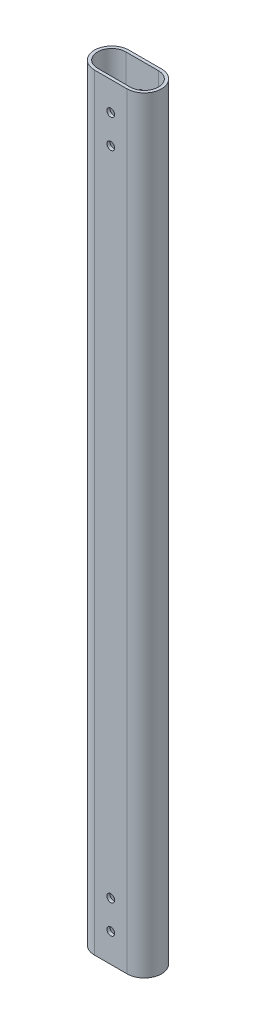
SolidWorks part; units mm, degrees
ref_plane "前基準面" through (0, 0, 0) normal (0, 0, 1) x (1, 0, 0)
ref_plane "上基準面" through (0, 0, 0) normal (0, 1, 0) x (1, 0, 0)
ref_plane "右基準面" through (0, 0, 0) normal (1, 0, 0) x (0, 0, -1)
sketch "草圖1" plane through (0, 0, 0) normal (0, 1, 0) x (1, 0, 0)
  line L0 (8.5, -7.4) -> (-8.5, -7.4)
  line L1 (8.5, 9) -> (-8.5, 9)
  line L2 (8.5, 7.4) -> (-8.5, 7.4)
  line L3 (8.5, -9) -> (-8.5, -9)
  line L4 (8.5, -7.4) -> (8.5, 7.4) construction
  line L5 (8.5, 9) -> (-8.5, -9) construction
  line L6 (8.5, -9) -> (-8.5, 9) construction
  line L7 (-8.5, -7.4) -> (-8.5, 7.4) construction
  arc A0 (-8.5, 9) -> (-8.5, -9) centre (-8.5, 0) ccw
  arc A1 (8.5, -9) -> (8.5, 9) centre (8.5, 0) ccw
  arc A2 (-8.5, 7.4) -> (-8.5, -7.4) centre (-8.5, 0) ccw
  arc A3 (8.5, -7.4) -> (8.5, 7.4) centre (8.5, 0) ccw
  point P0 (0, 0)
  dimension "D4" = 9
  dimension "D5" = 9
  dimension "D1" = 17
  dimension "D2" = 18
  dimension "D3" = 1.6
extrude "填料-伸長1" add sketch "草圖1" along normal blind 400
hole_wizard "#10-32 螺紋孔1" positions "草圖3" profile "草圖4" tap size "#10-32" standard "Ansi 英吋" end condition through all
sketch "草圖3" plane through (0, 0, 9) normal (0, 0, 1) x (1, 0, 0)
  line L0 (0, 0) -> (0, 400) construction
  line L1 (-8.5, 0) -> (8.5, 0) construction
  line L2 (-8.5, 400) -> (8.5, 400) construction
  point P0 (0, 30)
  point P8 (0, 15)
  point P11 (0, 385)
  point P13 (0, 370)
  dimension "D1" = 30
  dimension "D2" = 15
  dimension "D3" = 15
  dimension "D4" = 15
sketch "草圖4" plane through (0, 30, 9) normal (1, 0, 0) x (0, -1, 0)
  line L0 (0, 0) -> (0, 18)
  line L1 (0, 18) -> (2.0193, 18)
  line L2 (2.0193, 18) -> (2.0193, 0)
  line L5 (2.0193, 0) -> (0, 0)
  line L11 (0, -6.35) -> (0, 107.95) construction
  dimension "貫穿螺孔鑽直徑" = 4.0386
  dimension "貫穿螺孔鑽深度" = 18
cosmetic thread "鑽孔螺紋1" parameters "D2"=4.826
cosmetic thread "鑽孔螺紋2" parameters "D2"=4.826
cosmetic thread "鑽孔螺紋3" parameters "D2"=4.826
cosmetic thread "鑽孔螺紋4" parameters "D2"=4.826
